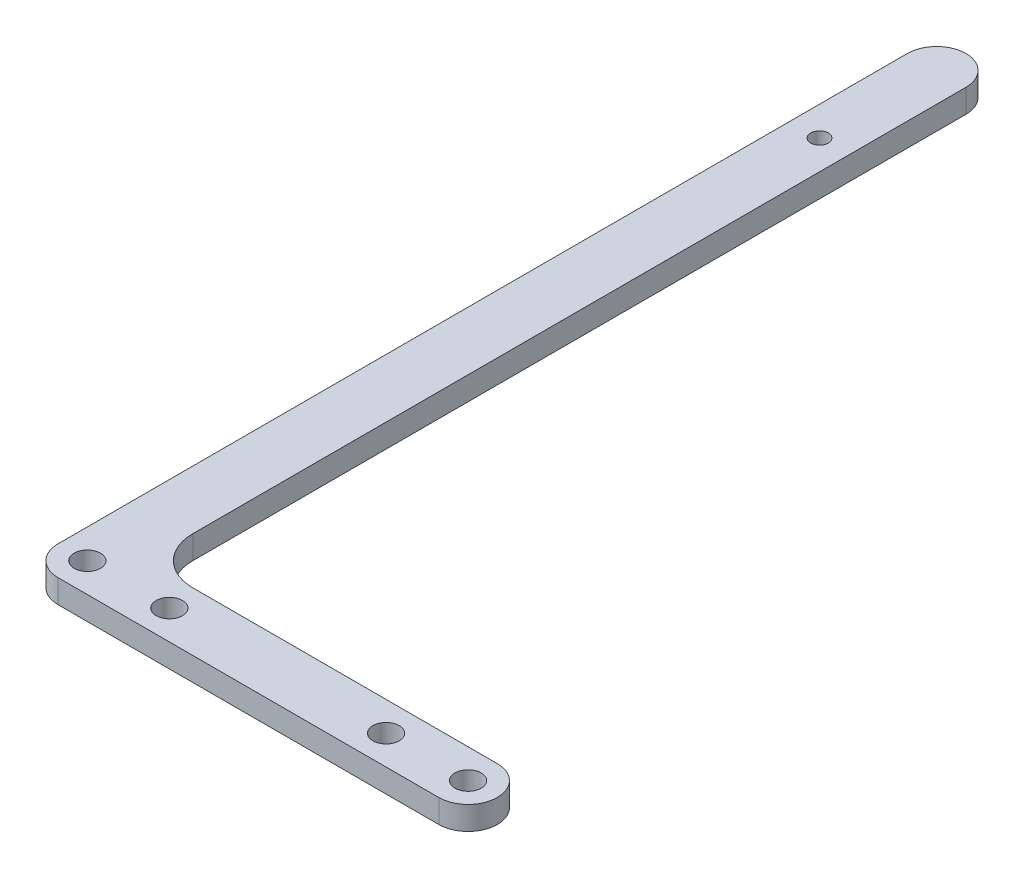
SolidWorks part; units mm, degrees
ref_plane "Front" through (0, 0, 0) normal (0, 0, 1) x (1, 0, 0)
ref_plane "Top" through (0, 0, 0) normal (0, 1, 0) x (1, 0, 0)
ref_plane "Right" through (0, 0, 0) normal (1, 0, 0) x (0, 0, -1)
sketch "Sketch1" plane through (0, 0, 0) normal (0, 1, 0) x (1, 0, 0)
  line L0 (10, 140) -> (10, 0)
  line L1 (10, 0) -> (0, 0)
  line L2 (0, 0) -> (0, 140)
  arc A0 (0, 140) -> (10, 140) centre (5, 140) cw
  circle A1 centre (5, 120) radius 1.5
  dimension "D1" = 10
  dimension "D3" = 120
  dimension "D2" = 3
  dimension "D4" = 20
extrude "Boss-Extrude1" add sketch "Sketch1" along normal blind 4
sketch "Sketch2" plane through (0, 4, 0) normal (0, 1, 0) x (1, 0, 0)
  line L0 (10, 0) -> (70, 0)
  line L1 (70, -10) -> (0, -10)
  line L2 (0, -10) -> (0, 0)
  line L3 (70, -5) -> (0, -5) construction
  arc A0 (70, 0) -> (70, -10) centre (70, -5) cw
  circle A1 centre (5, -5) radius 2.25
  circle A2 centre (19, -5) radius 2.25
  circle A3 centre (56, -5) radius 2.25
  circle A4 centre (70, -5) radius 2.25
  dimension "D3" = 4.5
  dimension "D4" = 4.5
  dimension "D5" = 4.5
  dimension "D6" = 4.5
  dimension "D1" = 10
  dimension "D7" = 14
  dimension "D8" = 14
  dimension "D9" = 5
  dimension "D2" = 60
extrude "Boss-Extrude2" add sketch "Sketch2" against normal blind 4
fillet "Fillet1" radius 8 1 edges at (10, 2, 0)
fillet "Fillet2" radius 5 1 edges at (0, 2, 10)
equation "\"D4@Sketch2\"=\"D3@Sketch2\""
equation "\"D5@Sketch2\"=\"D3@Sketch2\""
equation "\"D6@Sketch2\"=\"D3@Sketch2\""
equation "\"D8@Sketch2\"=\"D7@Sketch2\""
equation "\"D9@Sketch2\"=\"D1@Sketch2\"/2"
